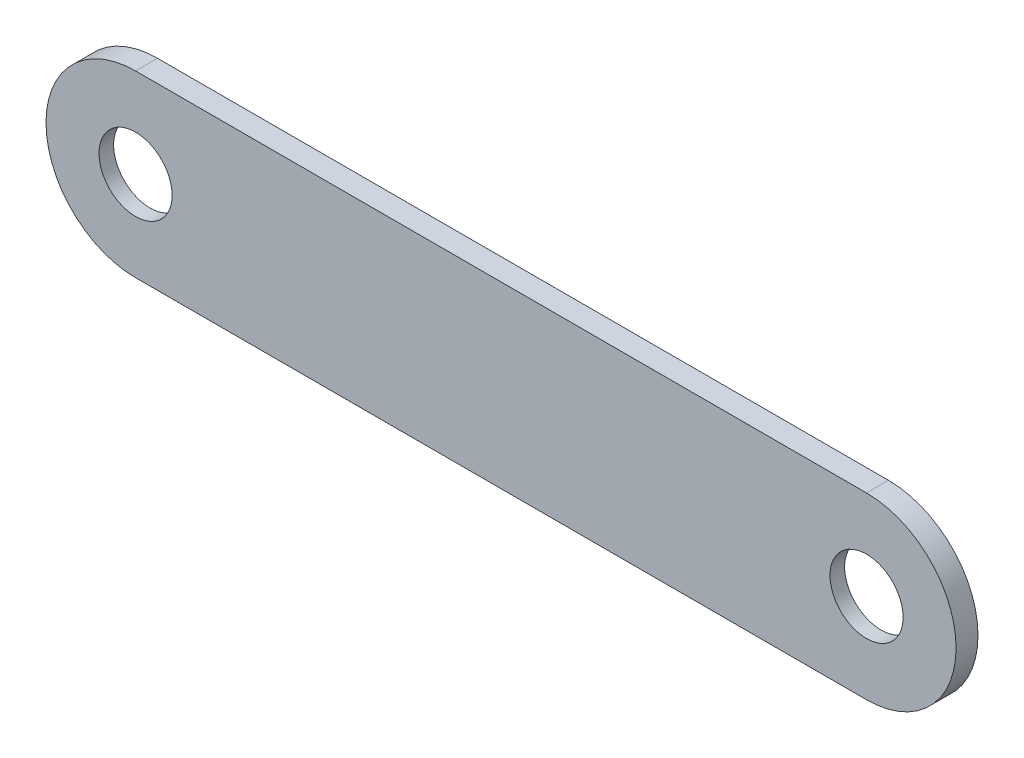
SolidWorks part; units mm, degrees
ref_plane "前视基准面" through (0, 0, 0) normal (0, 0, 1) x (1, 0, 0)
ref_plane "上视基准面" through (0, 0, 0) normal (0, 1, 0) x (1, 0, 0)
ref_plane "右视基准面" through (0, 0, 0) normal (1, 0, 0) x (0, 0, -1)
sketch "草图1" plane through (0, 0, 0) normal (0, 0, 1) x (1, 0, 0)
  line L0 (0, 12.25) -> (100, 12.25)
  line L1 (0, -12.25) -> (100, -12.25)
  arc A0 (0, 12.25) -> (0, -12.25) centre (0, 0) ccw
  arc A1 (100, -12.25) -> (100, 12.25) centre (100, 0) ccw
  circle A2 centre (0, 0) radius 5
  circle A10 centre (100, 0) radius 5
  point P20 (100, 0)
  dimension "D1" = 24.5
  dimension "D3" = 10
  dimension "D4" = 10
  dimension "D2" = 2
extrude "凸台-拉伸1" add sketch "草图1" along normal blind 3
ref_plane "基准面6" through (0, 0, 1) normal (0, 0, 1) x (1, 0, 0)
sketch "草图4" plane through (0, 0, 1) normal (0, 0, 1) x (1, 0, 0)
  circle A0 centre (0, 0) radius 7.5
  circle A1 centre (100, 0) radius 7.5
  dimension "D1" = 15
  dimension "D2" = 15
extrude "切除-拉伸3" cut sketch "草图4" against normal blind 3
